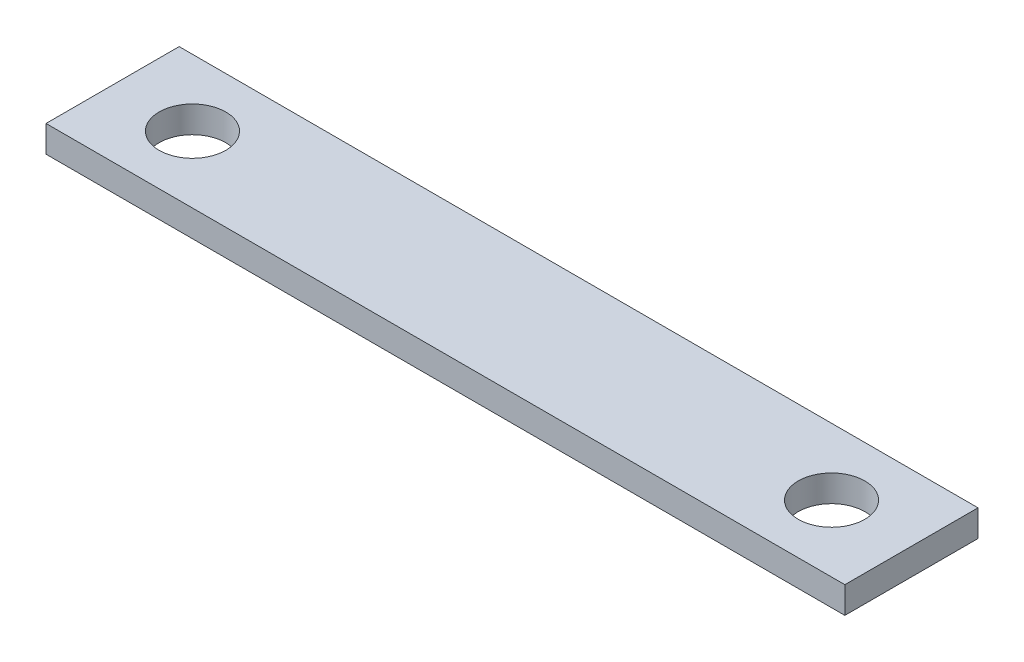
SolidWorks part; units mm, degrees
ref_plane "Front Plane" through (0, 0, 0) normal (0, 0, 1) x (1, 0, 0)
ref_plane "Top Plane" through (0, 0, 0) normal (0, 1, 0) x (1, 0, 0)
ref_plane "Right Plane" through (0, 0, 0) normal (1, 0, 0) x (0, 0, -1)
sketch "Sketch1" plane through (0, 0, 0) normal (0, 1, 0) x (1, 0, 0)
  line L0 (38.1, 12.7) -> (38.1, 0) construction
  line L1 (0, 0) -> (76.2, 0)
  line L2 (0, 0) -> (0, 12.7)
  line L3 (0, 12.7) -> (76.2, 12.7)
  line L4 (76.2, 0) -> (76.2, 12.7)
  line L5 (38.1, 6.35) -> (7.62, 6.35) construction
  circle A0 centre (7.62, 6.35) radius 3.175
  circle A1 centre (68.58, 6.35) radius 3.175
  dimension "D1" = 76.2
  dimension "D2" = 12.7
extrude "Boss-Extrude2" add sketch "Sketch1" along normal blind 2.54
